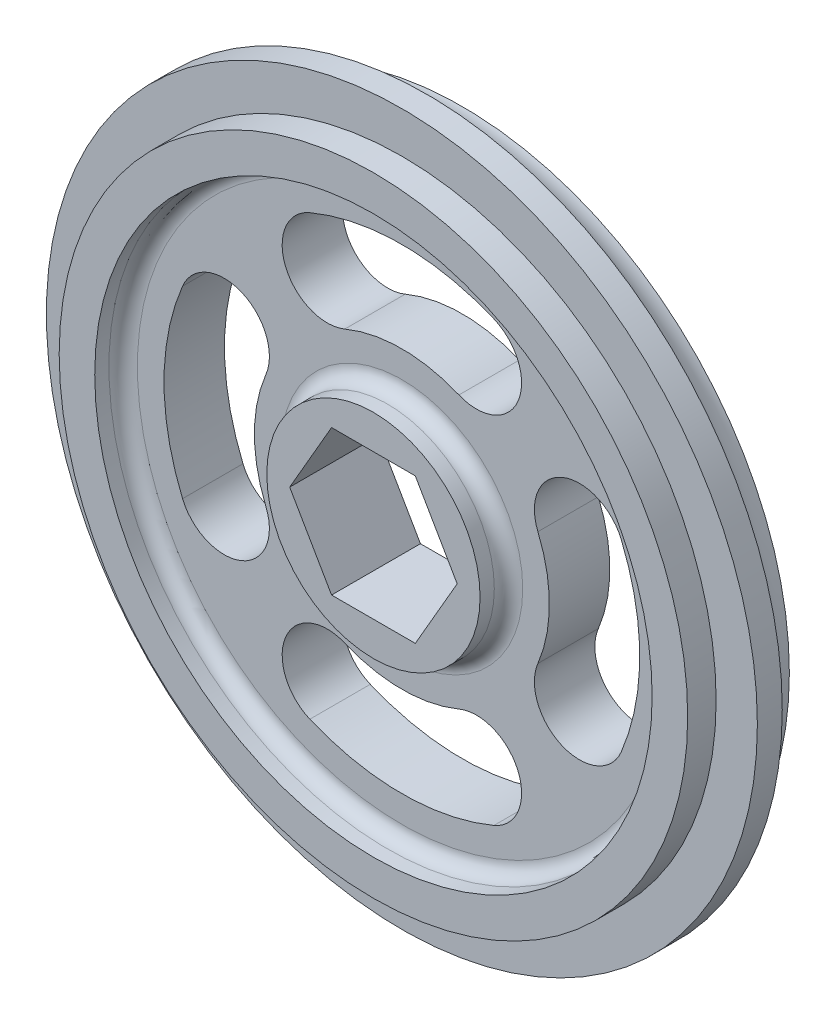
SolidWorks part; units mm, degrees
ref_plane "Front Plane" through (0, 0, 0) normal (0, 0, 1) x (1, 0, 0)
ref_plane "Top Plane" through (0, 0, 0) normal (0, 1, 0) x (1, 0, 0)
ref_plane "Right Plane" through (0, 0, 0) normal (1, 0, 0) x (0, 0, -1)
sketch "Sketch1" plane through (0, 0, 0) normal (0, 0, 1) x (1, 0, 0)
  line L1 (-7.479, 0) -> (-3.7395, -6.477)
  line L2 (-3.7395, -6.477) -> (3.7395, -6.477)
  line L3 (3.7395, -6.477) -> (7.479, 0)
  line L4 (7.479, 0) -> (3.7395, 6.477)
  line L5 (3.7395, 6.477) -> (-3.7395, 6.477)
  line L6 (-3.7395, 6.477) -> (-7.479, 0)
  circle A0 centre (0, 0) radius 6.477 construction
  circle A1 centre (0, 0) radius 31.75
  dimension "D1" = 63.5
  dimension "D2" = 12.954
extrude "Hex Axel Cutout & Outside Rim" add sketch "Sketch1" along normal blind 15.875
sketch "Sketch3" plane through (0, 0, 15.875) normal (0, 0, 1) x (1, 0, 0)
  circle A0 centre (0, 0) radius 28.067
  circle A1 centre (0, 0) radius 31.75
  circle A2 centre (0, 0) radius 31.75 construction
  dimension "D1" = 56.134
extrude "Pipe Step" cut sketch "Sketch3" against normal blind 2.54
ref_plane "Mid Plane" through (0, 0, 7.9375) normal (0, 0, 1) x (1, 0, 0)
mirror "Step Mirror" about plane through (0, 0, 7.9375) normal (0, 0, 1) of "Pipe Step"
ref_axis "Center Axis" through (0, 0, 13.335) along (0, 0, -1)
sketch "Sketch4" plane through (0, 0, 0) normal (1, 0, 0) x (0, 0, -1)
  line L0 (-2.54, -31.75) -> (-2.54, 31.75) construction
  line L1 (-2.54, -31.75) -> (-2.54, 31.75) construction
  line L2 (-13.335, 31.75) -> (-13.335, -31.75) construction
  line L3 (-13.335, 31.75) -> (-13.335, -31.75) construction
  line L4 (-2.54, 31.75) -> (-13.335, 31.75) construction
  line L5 (-4.7625, 31.75) -> (-11.1125, 31.75)
  line L6 (-4.7625, 31.75) -> (-11.1125, 31.75) construction
  line L7 (-7.9375, 31.75) -> (-7.9375, 29.21) construction
  arc A1 (-4.7625, 31.75) -> (-11.1125, 31.75) centre (-7.9375, 32.4644) cw
  dimension "D1" = 6.35
  dimension "D2" = 2.54
revolve "Poly Cord Groove" cut sketch "Sketch4" angle 360 about axis through (0, 0, 13.335) along (0, 0, -1)
sketch "Sketch5" plane through (0, 0, 0) normal (0, 0, -1) x (-1, 0, 0)
  circle A0 centre (0, 0) radius 9.525
  circle A1 centre (0, 0) radius 24.892
  circle A2 centre (0, 0) radius 28.067 construction
  dimension "D1" = 3.175
extrude "Spoke Step" cut sketch "Sketch5" against normal blind 2.54
mirror "Spoke Step Mirror" about plane through (0, 0, 7.9375) normal (0, 0, 1) of "Spoke Step"
sketch "Sketch6" plane through (0, 0, 13.335) normal (0, 0, 1) x (1, 0, 0)
  line L0 (9.525, 0) -> (24.892, 0) construction
  arc A2 (15.8685, -6.6575) -> (15.8685, 6.6575) centre (0, 0) ccw construction
  arc A3 (19.5892, -8.2184) -> (19.5892, 8.2184) centre (0, 0) ccw
  arc A4 (12.1479, -5.0965) -> (12.1479, 5.0965) centre (0, 0) ccw
  arc A5 (12.1479, -5.0965) -> (19.5892, -8.2184) centre (15.8685, -6.6575) ccw
  arc A6 (19.5892, 8.2184) -> (12.1479, 5.0965) centre (15.8685, 6.6575) ccw
  circle A7 centre (0, 0) radius 9.525 construction
  circle A8 centre (0, 0) radius 24.892 construction
  arc A9 (-6.6575, -15.8685) -> (6.6575, -15.8685) centre (0, 0) ccw construction
  arc A10 (-8.2184, -19.5892) -> (8.2184, -19.5892) centre (0, 0) ccw
  arc A11 (-5.0965, -12.1479) -> (5.0965, -12.1479) centre (0, 0) ccw
  arc A12 (-5.0965, -12.1479) -> (-8.2184, -19.5892) centre (-6.6575, -15.8685) ccw
  arc A13 (8.2184, -19.5892) -> (5.0965, -12.1479) centre (6.6575, -15.8685) ccw
  arc A14 (-15.8685, 6.6575) -> (-15.8685, -6.6575) centre (0, 0) ccw construction
  arc A15 (-19.5892, 8.2184) -> (-19.5892, -8.2184) centre (0, 0) ccw
  arc A16 (-12.1479, 5.0965) -> (-12.1479, -5.0965) centre (0, 0) ccw
  arc A17 (-12.1479, 5.0965) -> (-19.5892, 8.2184) centre (-15.8685, 6.6575) ccw
  arc A18 (-19.5892, -8.2184) -> (-12.1479, -5.0965) centre (-15.8685, -6.6575) ccw
  arc A19 (6.6575, 15.8685) -> (-6.6575, 15.8685) centre (0, 0) ccw construction
  arc A20 (8.2184, 19.5892) -> (-8.2184, 19.5892) centre (0, 0) ccw
  arc A21 (5.0965, 12.1479) -> (-5.0965, 12.1479) centre (0, 0) ccw
  arc A22 (5.0965, 12.1479) -> (8.2184, 19.5892) centre (6.6575, 15.8685) ccw
  arc A23 (-8.2184, 19.5892) -> (-5.0965, 12.1479) centre (-6.6575, 15.8685) ccw
  point P3 (17.2085, 0)
  point P14 (17.2085, 0)
  point P20 (0, -17.2085)
  point P28 (-17.2085, 0)
  point P35 (0, 17.2085)
  point P40 (0, 0)
  point P42 (0, 0)
  dimension "D1" = 4
extrude "Slots" cut sketch "Sketch6" against normal through all
fillet "Fillet1" radius 1.27 4 edges at (-9.525, 0, 13.335) (-24.892, 0, 13.335) (-9.525, 0, 2.54) (-24.892, 0, 2.54)
sketch "Sketch7" plane through (0, 0, 7.9375) normal (0, 0, 1) x (1, 0, 0)
  line L1 (83.5497, 87.9569) -> (-79.5373, 87.9569)
  line L2 (83.5497, 87.9569) -> (83.5497, -80.7019)
  line L3 (83.5497, -80.7019) -> (-79.5373, -80.7019)
  line L4 (-79.5373, 87.9569) -> (-79.5373, -80.7019)
extrude "MidCut" cut sketch "Sketch7" against normal through all
